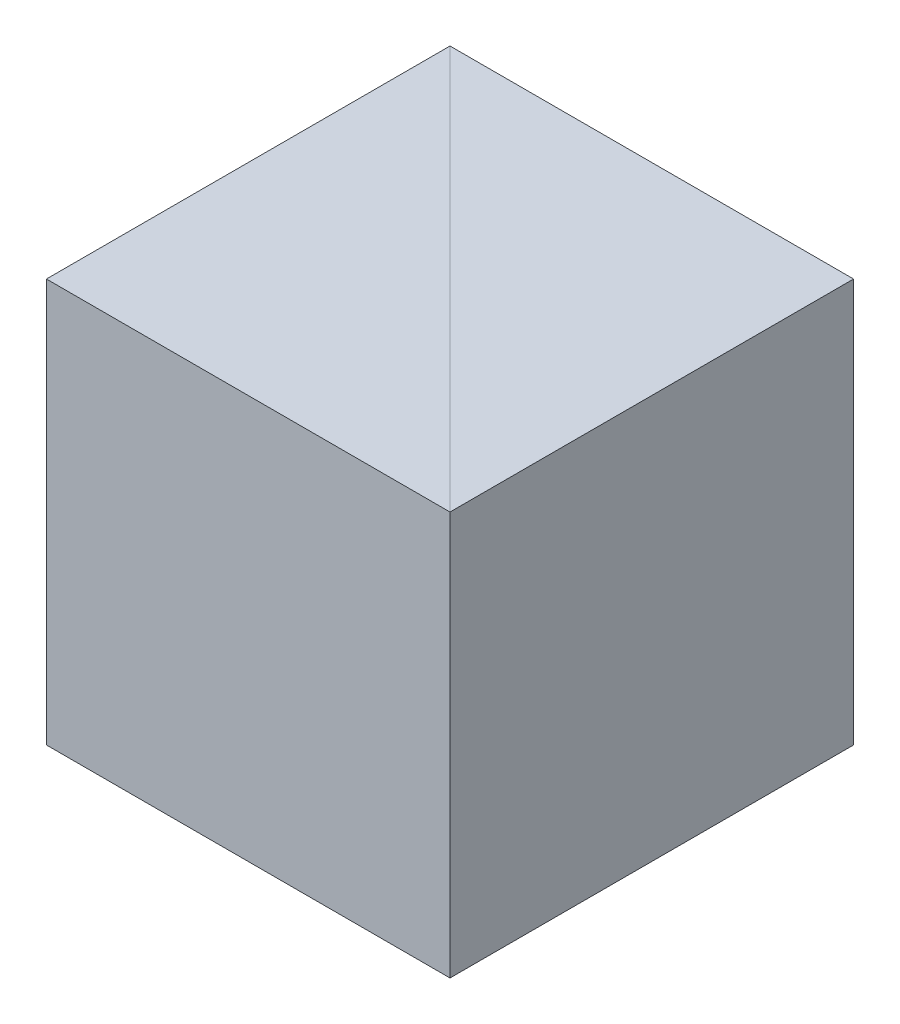
SolidWorks part; units mm, degrees
ref_plane "前视基准面" through (0, 0, 0) normal (0, 0, 1) x (1, 0, 0)
ref_plane "上视基准面" through (0, 0, 0) normal (0, 1, 0) x (1, 0, 0)
ref_plane "右视基准面" through (0, 0, 0) normal (1, 0, 0) x (0, 0, -1)
sketch "草图1" plane through (0, 0, 0) normal (0, 1, 0) x (1, 0, 0)
  line L0 (0, 0) -> (0, 12.7)
  line L1 (0, 12.7) -> (-12.7, 12.7)
  line L2 (-12.7, 12.7) -> (0, 0)
  dimension "D1" = 12.7
  dimension "D2" = 12.7
extrude "凸台-拉伸1" add sketch "草图1" along normal blind 12.7
sketch "草图2" plane through (0, 0, 0) normal (0, -1, 0) x (1, 0, 0)
  line L0 (-12.7, -12.7) -> (-12.7, 0)
  line L1 (-12.7, 0) -> (0, 0)
  line L2 (0, 0) -> (-12.7, -12.7)
extrude "凸台-拉伸2" add sketch "草图2" against normal blind 12.7 separate body
